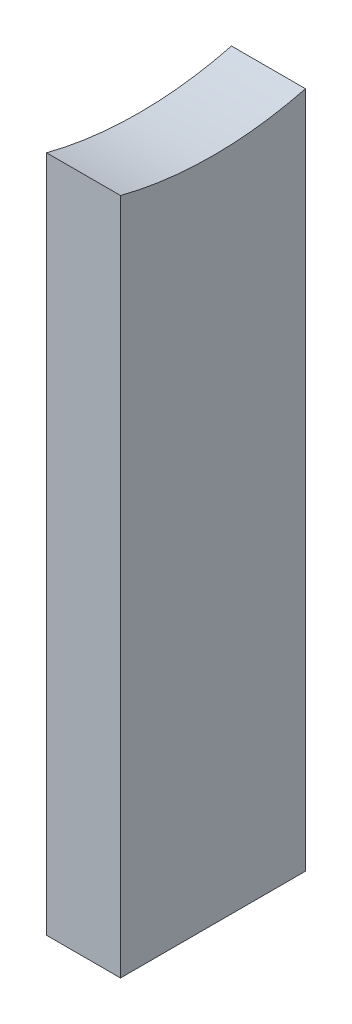
SolidWorks part; units mm, degrees
ref_plane "Front Plane" through (0, 0, 0) normal (0, 0, 1) x (1, 0, 0)
ref_plane "Top Plane" through (0, 0, 0) normal (0, 1, 0) x (1, 0, 0)
ref_plane "Right Plane" through (0, 0, 0) normal (1, 0, 0) x (0, 0, -1)
sketch "Sketch1" plane through (0, 0, 0) normal (1, 0, 0) x (0, 0, -1)
  line L0 (-6.35, -24.5934) -> (-6.35, -71.12)
  line L5 (-6.35, -71.12) -> (6.35, -71.12)
  line L6 (6.35, -71.12) -> (6.35, -24.5934)
  arc A2 (-6.35, -24.5934) -> (6.35, -24.5934) centre (0, 0) ccw
  point P8 (0, -25.4)
  point P9 (0, -71.12)
  dimension "D2" = 25.4
  dimension "D1" = 45.72
  dimension "D3" = 12.7
extrude "Boss-Extrude1" add sketch "Sketch1" along normal blind 5.08
equation "\"MDF\"= 0.2in"
equation "\"Foamcore\"= 0.2in"
equation "\"TubeR\"= 0.8in"
equation "\"D2@Sketch1\"=\"TubeR\"+\"Foamcore\""
equation "\"D1@Boss-Extrude1\"=\"Foamcore\""
